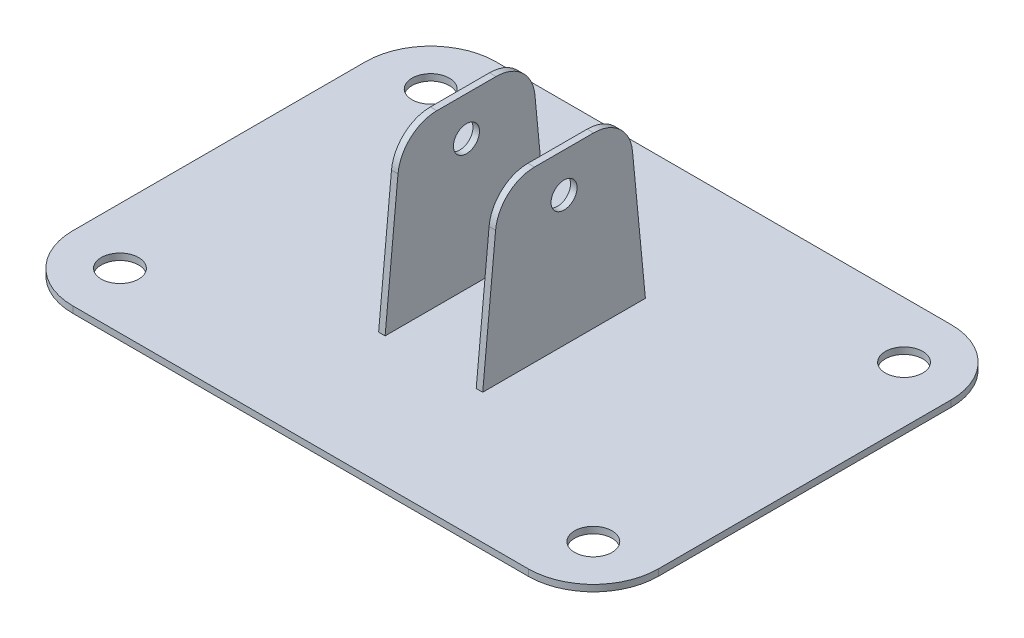
SolidWorks part; units mm, degrees
material "ABS"
ref_plane "Front Plane" through (0, 0, 0) normal (0, 0, 1) x (1, 0, 0)
ref_plane "Top Plane" through (0, 0, 0) normal (0, 1, 0) x (1, 0, 0)
ref_plane "Right Plane" through (0, 0, 0) normal (1, 0, 0) x (0, 0, -1)
sketch "Sketch1" plane through (0, 0, 0) normal (0, 1, 0) x (1, 0, 0)
  line L0 (-45, 0) -> (45, 0) construction
  line L1 (-45, -32.5) -> (45, -32.5)
  line L2 (-45, -32.5) -> (-45, 32.5)
  line L3 (-45, 32.5) -> (45, 32.5)
  line L4 (45, -32.5) -> (45, 32.5)
  line L5 (-45, -32.5) -> (45, 32.5) construction
  line L6 (-45, 32.5) -> (45, -32.5) construction
  line L7 (0, 32.5) -> (0, -32.5) construction
  line L8 (-36.375, 23.875) -> (36.375, 23.875) construction
  line L9 (-36.375, 23.875) -> (-36.375, -23.875) construction
  line L10 (-36.375, -23.875) -> (36.375, -23.875) construction
  circle A0 centre (-36.375, 23.875) radius 2.875
  circle A1 centre (36.375, 23.875) radius 2.875
  circle A2 centre (36.375, -23.875) radius 2.875
  circle A3 centre (-36.375, -23.875) radius 2.875
  point P0 (0, 0)
  point P14 (0, 23.875)
  point P16 (-36.375, 21)
  point P20 (-36.375, 0)
  point P21 (-36.375, -21)
  point P22 (-33.5, 23.875)
  point P23 (33.5, 23.875)
  point P26 (36.7653, 22.4452)
  dimension "D3" = 5.75
  dimension "D1" = 90
  dimension "D2" = 65
  dimension "D4" = 42
  dimension "D5" = 67
  dimension "D6" = 72.75
  dimension "D7" = 47.75
extrude "Boss-Extrude1" add sketch "Sketch1" along normal blind 1
fillet "Fillet1" radius 10 4 edges at (-45, 0.5, 32.5) (-45, 0.5, -32.5) (45, 0.5, -32.5) (45, 0.5, 32.5)
sketch "Sketch2" plane through (45, 0, 0) normal (1, 0, 0) x (0, 0, -1)
  line L0 (0, 0) -> (0, 35.2542) construction
  line L1 (-12.5, 1) -> (-10, 27)
  line L2 (-22.5, 1) -> (22.5, 1) construction
  line L3 (-10, 27) -> (10, 27)
  line L4 (0, 21) -> (-10.5769, 21) construction
  line L5 (12.5, 1) -> (10, 27)
  line L6 (-12.5, 1) -> (12.5, 1)
  circle A0 centre (0, 21) radius 2
  point P12 (0, 27)
  dimension "D4" = 6
  dimension "D5" = 4
  dimension "D1" = 25
  dimension "D2" = 26
  dimension "D3" = 20
extrude "Boss-Extrude2" add sketch "Sketch2" against normal blind 1 from offset 37 offset against normal yes
fillet "Fillet2" radius 6 2 edges at (7.5, 27, 10) (7.5, 27, -10)
ref_plane "Plane1" through (0, 0, 0) normal (-1, 0, 0) x (0, 0, 1)
mirror "Mirror1" about plane through (0, 0, 0) normal (-1, 0, 0) of "Boss-Extrude2", "Fillet2"
